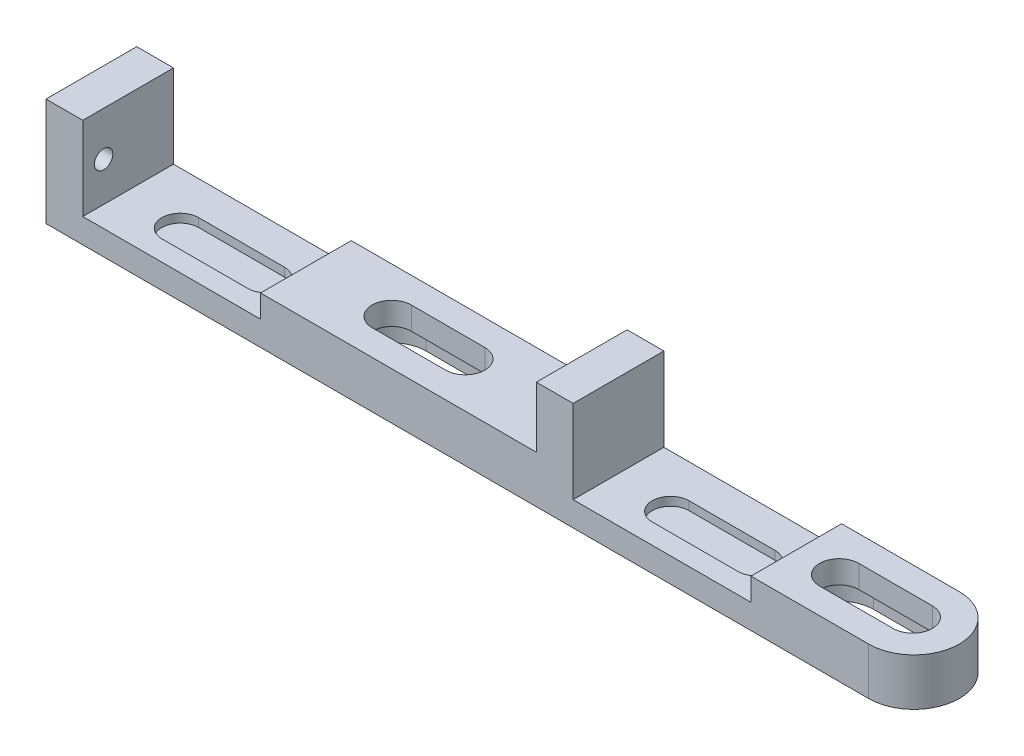
SolidWorks part; units mm, degrees
material "6061 Alloy"
ref_plane "Front Plane" through (0, 0, 0) normal (0, 0, 1) x (1, 0, 0)
ref_plane "Top Plane" through (0, 0, 0) normal (0, 1, 0) x (1, 0, 0)
ref_plane "Right Plane" through (0, 0, 0) normal (1, 0, 0) x (0, 0, -1)
sketch "Sketch1" plane through (0, 0, 0) normal (0, 0, 1) x (1, 0, 0)
  line L0 (0, 0) -> (0, 8.8)
  line L1 (0, 0) -> (70.8, 0)
  line L8 (70.8, 0) -> (70.8, 3.85)
  line L10 (0, 8.8) -> (3, 8.8)
  line L11 (3, 8.8) -> (3, 2)
  line L20 (40, 3.85) -> (40, 8.8)
  line L21 (40, 8.8) -> (43, 8.8)
  line L22 (43, 8.8) -> (43, 2)
  line L23 (40, 3.85) -> (17.5, 3.85)
  line L24 (17.5, 3.85) -> (17.5, 2)
  line L25 (17.5, 2) -> (3, 2)
  line L26 (70.8, 3.85) -> (57.5, 3.85)
  line L27 (57.5, 3.85) -> (57.5, 2)
  line L28 (57.5, 2) -> (43, 2)
  dimension "D1" = 3
  dimension "D2" = 2
  dimension "D3" = 8.8
  dimension "D4" = 3.85
  dimension "D5" = 14.5
  dimension "D6" = 3
  dimension "D7" = 40
  dimension "D8" = 14.5
  dimension "D10" = 70.8
extrude "Boss-Extrude1" add sketch "Sketch1" along normal blind 7.4
sketch "Sketch3" plane through (0, 3.85, 0) normal (0, 1, 0) x (1, 0, 0)
  line L0 (30.5, -3.7) -> (24.5, -3.7) construction
  line L1 (30.5, -5.3) -> (24.5, -5.3)
  line L2 (30.5, -2.1) -> (24.5, -2.1)
  line L3 (67, -3.7) -> (61, -3.7) construction
  line L4 (67, -5.3) -> (61, -5.3)
  line L5 (67, -2.1) -> (61, -2.1)
  line L6 (40, -7.4) -> (40, 0) construction
  arc A0 (30.5, -5.3) -> (30.5, -2.1) centre (30.5, -3.7) ccw
  arc A1 (24.5, -2.1) -> (24.5, -5.3) centre (24.5, -3.7) ccw
  arc A2 (67, -5.3) -> (67, -2.1) centre (67, -3.7) ccw
  arc A3 (61, -2.1) -> (61, -5.3) centre (61, -3.7) ccw
  point P2 (27.5, -3.7)
  point P7 (64, -3.7)
  point P21 (40, -3.7)
  dimension "D2" = 1.6
  dimension "D1" = 6
  dimension "D3" = 12.5
  dimension "D4" = 36.5
extrude "Cut-Extrude1" cut sketch "Sketch3" against normal blind 10
sketch "Sketch4" plane through (0, 0, 0) normal (0, -1, 0) x (1, 0, 0)
  line L0 (24.5, 5.3) -> (30.5, 5.3) construction
  line L1 (30.5, 2.1) -> (24.5, 2.1) construction
  line L2 (24.5, 5.3) -> (30.5, 5.3)
  line L3 (30.5, 2.1) -> (24.5, 2.1)
  line L4 (61, 5.3) -> (67, 5.3) construction
  line L5 (67, 2.1) -> (61, 2.1) construction
  line L6 (61, 5.3) -> (67, 5.3)
  line L7 (67, 2.1) -> (61, 2.1)
  line L8 (24.5, 6.5) -> (30.5, 6.5)
  line L9 (30.5, 0.9) -> (24.5, 0.9)
  line L10 (61, 6.5) -> (67, 6.5)
  line L11 (67, 0.9) -> (61, 0.9)
  arc A0 (30.5, 2.1) -> (30.5, 5.3) centre (30.5, 3.7) ccw construction
  arc A1 (24.5, 5.3) -> (24.5, 2.1) centre (24.5, 3.7) ccw construction
  arc A2 (30.5, 2.1) -> (30.5, 5.3) centre (30.5, 3.7) ccw
  arc A3 (24.5, 5.3) -> (24.5, 2.1) centre (24.5, 3.7) ccw
  arc A4 (61, 5.3) -> (61, 2.1) centre (61, 3.7) ccw construction
  arc A5 (67, 2.1) -> (67, 5.3) centre (67, 3.7) ccw construction
  arc A6 (61, 5.3) -> (61, 2.1) centre (61, 3.7) ccw
  arc A7 (67, 2.1) -> (67, 5.3) centre (67, 3.7) ccw
  arc A8 (30.5, 0.9) -> (30.5, 6.5) centre (30.5, 3.7) ccw
  arc A9 (24.5, 6.5) -> (24.5, 0.9) centre (24.5, 3.7) ccw
  arc A10 (67, 0.9) -> (67, 6.5) centre (67, 3.7) ccw
  arc A11 (61, 6.5) -> (61, 0.9) centre (61, 3.7) ccw
  dimension "D1" = 1.2
  dimension "D2" = 1.2
extrude "Cut-Extrude2" cut sketch "Sketch4" against normal blind 2
sketch "Sketch5" plane through (0, 0, 0) normal (-1, 0, 0) x (0, 0, 1)
  line L0 (7.4, 8.8) -> (0, 8.8) construction
  line L2 (7.4, 8.8) -> (7.4, 0) construction
  circle A0 centre (5.7, 5.2) radius 0.75
  dimension "D1" = 1.5
  dimension "D2" = 3.6
  dimension "D3" = 1.7
extrude "Cut-Extrude3" cut sketch "Sketch5" against normal up to next
sketch "Sketch6" plane through (0, 0, 0) normal (0, -1, 0) x (1, 0, 0)
  line L0 (70.8, 0) -> (70.8, 7.4)
  line L1 (70.8, 7.4) -> (70.8, 0) construction
  line L2 (70.8, 7.4) -> (67.1, 7.4)
  line L3 (0, 7.4) -> (70.8, 7.4) construction
  line L4 (0, 0) -> (70.8, 0) construction
  line L5 (67.1, 0) -> (70.8, 0)
  arc A0 (67.1, 7.4) -> (67.1, 0) centre (67.1, 3.7) cw
  line M13 (0, 0) -> (70.8, 0)
  line M14 (70.8, 0) -> (70.8, 7.4)
  line M15 (70.8, 7.4) -> (0, 7.4)
extrude "Cut-Extrude4" cut sketch "Sketch6" against normal blind 10 contours A0 M14 M13 | A0 L0 M15
sketch "Sketch7" [suppressed] plane through (0, 2, 0) normal (0, 1, 0) x (1, 0, 0)
  line L0 (54.8, -3.15) -> (47.8, -3.15) construction
  line L1 (54.8, -4.65) -> (47.8, -4.65)
  line L2 (54.8, -1.65) -> (47.8, -1.65)
  line L3 (14.8, -3.15) -> (7.8, -3.15) construction
  line L4 (14.8, -4.65) -> (7.8, -4.65)
  line L5 (14.8, -1.65) -> (7.8, -1.65)
  line L6 (57.5, 0) -> (43, 0) construction
  line L7 (57.5, -7.4) -> (57.5, 0) construction
  line L8 (17.5, -7.4) -> (17.5, 0) construction
  arc A0 (54.8, -4.65) -> (54.8, -1.65) centre (54.8, -3.15) ccw
  arc A1 (47.8, -1.65) -> (47.8, -4.65) centre (47.8, -3.15) ccw
  arc A2 (14.8, -4.65) -> (14.8, -1.65) centre (14.8, -3.15) ccw
  arc A3 (7.8, -1.65) -> (7.8, -4.65) centre (7.8, -3.15) ccw
  point P2 (51.3, -3.15)
  point P7 (11.3, -3.15)
  point P16 (50.25, 0)
  dimension "D2" = 1.5
  dimension "D4" = 2.7
  dimension "D5" = 2.7
  dimension "D1" = 3.15
  dimension "D3" = 7
extrude "Cut-Extrude5" [suppressed] cut sketch "Sketch7" against normal blind 0.7
sketch "Sketch8" plane through (0, 2, 0) normal (0, 1, 0) x (1, 0, 0)
  line L0 (7.8, -4.25) -> (14.8, -4.25) construction
  line L1 (7.8, -2.75) -> (14.8, -2.75)
  line L2 (7.8, -5.75) -> (14.8, -5.75)
  line L3 (47.8, -4.25) -> (54.8, -4.25) construction
  line L4 (47.8, -2.75) -> (54.8, -2.75)
  line L5 (47.8, -5.75) -> (54.8, -5.75)
  line L6 (17.5, -7.4) -> (17.5, 0) construction
  line L7 (17.5, -7.4) -> (3, -7.4) construction
  line L8 (57.5, -7.4) -> (57.5, 0) construction
  arc A0 (7.8, -2.75) -> (7.8, -5.75) centre (7.8, -4.25) ccw
  arc A1 (14.8, -5.75) -> (14.8, -2.75) centre (14.8, -4.25) ccw
  arc A2 (47.8, -2.75) -> (47.8, -5.75) centre (47.8, -4.25) ccw
  arc A3 (54.8, -5.75) -> (54.8, -2.75) centre (54.8, -4.25) ccw
  point P2 (11.3, -4.25)
  point P7 (51.3, -4.25)
  dimension "D2" = 2.7
  dimension "D3" = 1.5
  dimension "D5" = 2.7
  dimension "D1" = 7
  dimension "D4" = 3.15
extrude "Cut-Extrude6" cut sketch "Sketch8" against normal blind 0.7
